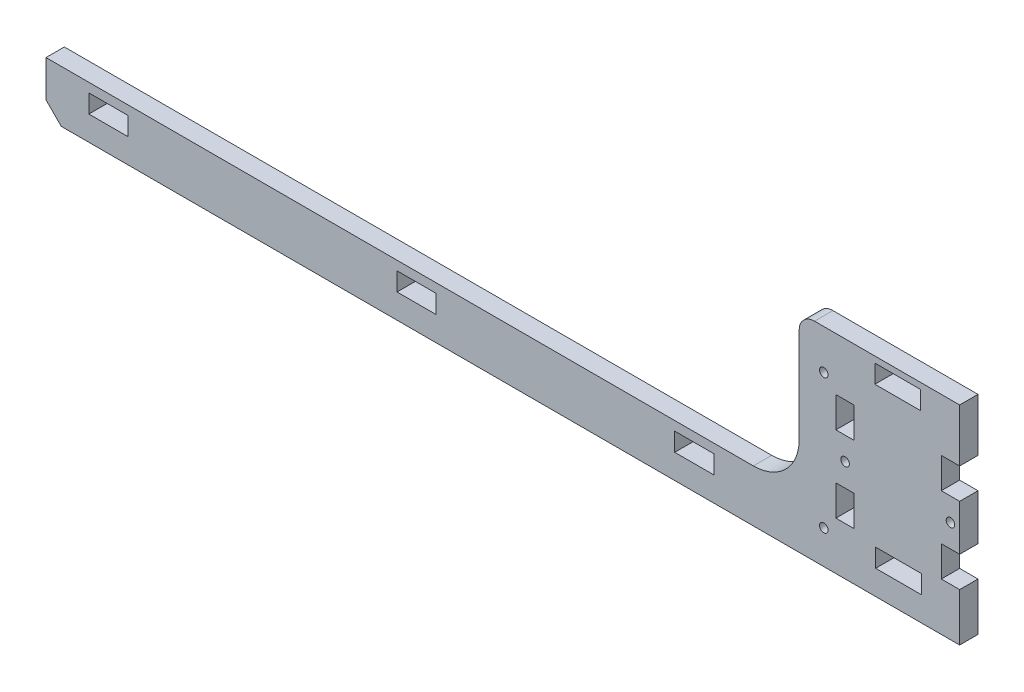
SolidWorks part; units mm, degrees
ref_plane "Front" through (0, 0, 0) normal (0, 0, 1) x (1, 0, 0)
ref_plane "Top" through (0, 0, 0) normal (0, 1, 0) x (1, 0, 0)
ref_plane "Right" through (0, 0, 0) normal (1, 0, 0) x (0, 0, -1)
sketch "Эскиз1" plane through (0, 0, 0) normal (0, 0, 1) x (1, 0, 0)
  line L46 (96.9208, 2) -> (96.9208, 25)
  line L55 (149.3892, 30) -> (149.3892, 20.7093)
  line L56 (149.3892, -30) -> (-144.3892, -30)
  line L57 (-144.3892, -30) -> (-149.3892, -25)
  line L58 (-149.3892, -25) -> (-149.3892, -13)
  line L59 (81.9208, -13) -> (-149.3892, -13)
  line L60 (-135.3886, -16) -> (-122.5886, -16)
  line L61 (-135.3886, -16) -> (-135.3886, -22)
  line L62 (-135.3886, -22) -> (-122.5886, -22)
  line L63 (-122.5886, -16) -> (-122.5886, -22)
  line L64 (-34.5886, -16) -> (-21.7886, -16)
  line L65 (-34.5886, -16) -> (-34.5886, -22)
  line L66 (-34.5886, -22) -> (-21.7886, -22)
  line L67 (-21.7886, -16) -> (-21.7886, -22)
  line L68 (56.2114, -16) -> (69.0114, -16)
  line L69 (56.2114, -16) -> (56.2114, -22)
  line L70 (56.2114, -22) -> (69.0114, -22)
  line L71 (69.0114, -16) -> (69.0114, -22)
  line L72 (121.9208, -16) -> (136.9208, -16)
  line L73 (121.9208, -16) -> (121.9208, -22)
  line L74 (121.9208, -22) -> (136.9208, -22)
  line L75 (136.9208, -16) -> (136.9208, -22)
  line L76 (143.3892, 20.7093) -> (149.3892, 20.7093)
  line L77 (143.3892, 20.7093) -> (143.3892, 10.7093)
  line L78 (143.3892, 10.7093) -> (149.3892, 10.7093)
  line L80 (143.3892, -4.2907) -> (149.3892, -4.2907)
  line L81 (143.3892, -4.2907) -> (143.3892, -14.2907)
  line L82 (143.3892, -14.2907) -> (149.3892, -14.2907)
  line L84 (108.9208, 20.7093) -> (114.9208, 20.7093)
  line L85 (108.9208, 20.7093) -> (108.9208, 10.7093)
  line L86 (108.9208, 10.7093) -> (114.9208, 10.7093)
  line L87 (114.9208, 20.7093) -> (114.9208, 10.7093)
  line L88 (108.9208, -14.2907) -> (114.9208, -14.2907)
  line L89 (108.9208, -14.2907) -> (108.9208, -4.2907)
  line L90 (108.9208, -4.2907) -> (114.9208, -4.2907)
  line L91 (114.9208, -14.2907) -> (114.9208, -4.2907)
  line L99 (149.3892, 30) -> (149.3892, 38)
  line L105 (149.3892, 10.7093) -> (149.3892, -4.2907)
  line L106 (149.3892, -14.2907) -> (149.3892, -30)
  line L107 (111.9208, 10.7093) -> (111.9208, -4.2907) construction
  line L108 (146.3892, 10.7093) -> (146.3892, -4.2907) construction
  line L109 (108.9208, 3.2093) -> (149.3892, 3.2405) construction
  line L110 (149.3892, 38) -> (101.9208, 38)
  line L111 (96.9208, 33) -> (96.9208, 25)
  line L113 (121.6558, 36) -> (136.6558, 36)
  line L114 (121.6558, 36) -> (121.6558, 30)
  line L115 (121.6558, 30) -> (136.6558, 30)
  line L116 (136.6558, 36) -> (136.6558, 30)
  arc A6 (96.9208, 2) -> (81.9208, -13) centre (81.9208, 2) cw
  circle A8 centre (104.9708, -19) radius 1.4
  circle A9 centre (104.9708, 25) radius 1.4
  circle A10 centre (111.9208, 3.2093) radius 1.4
  circle A11 centre (146.3892, 3.2093) radius 1.4
  arc A12 (101.9208, 38) -> (96.9208, 33) centre (101.9208, 33) ccw
  dimension "D1" = 2.8
  dimension "D2" = 2.8
  dimension "D6" = 5
  dimension "D3" = 8
  dimension "D7" = 2
  dimension "D8" = 6
  dimension "D9" = 15
extrude "Бобышка-Вытянуть1" add sketch "Эскиз1" along normal blind 6
